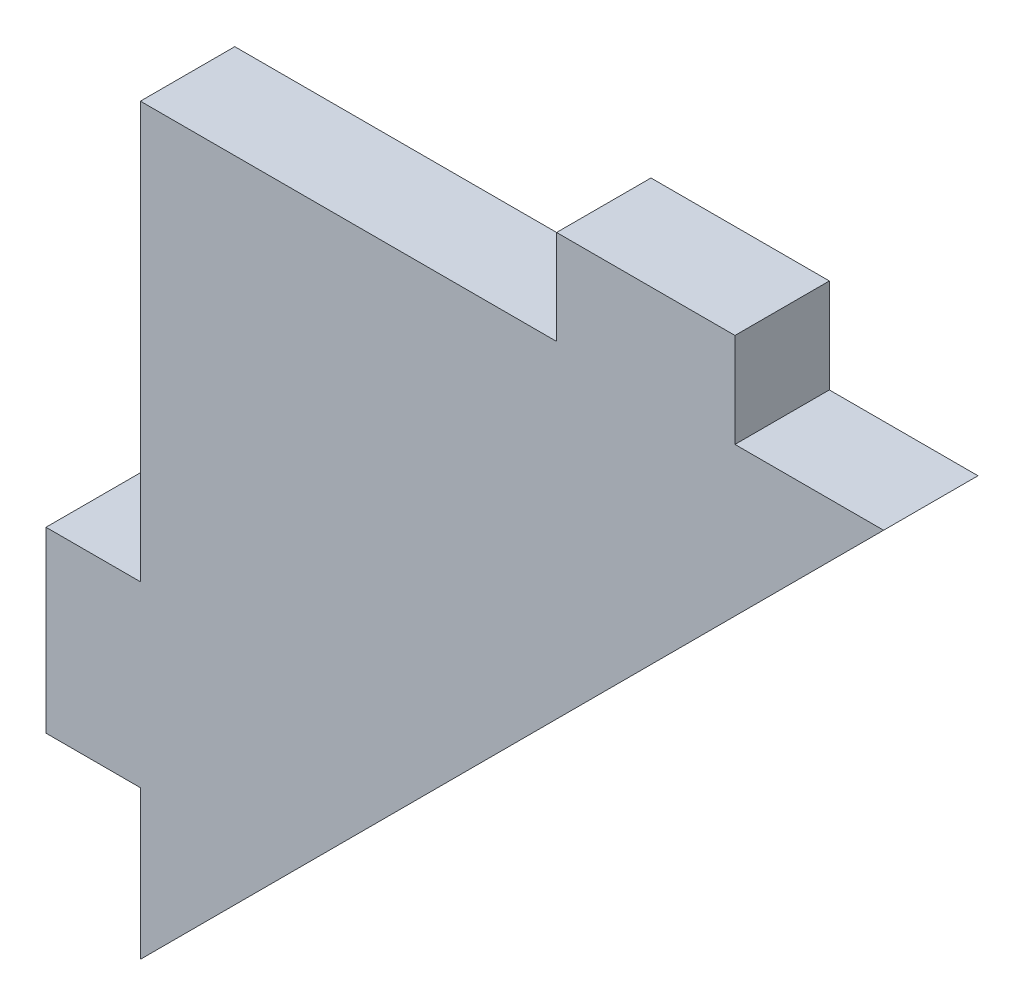
SolidWorks part; units mm, degrees
ref_plane "Front Plane" through (0, 0, 0) normal (0, 0, 1) x (1, 0, 0)
ref_plane "Top Plane" through (0, 0, 0) normal (0, 1, 0) x (1, 0, 0)
ref_plane "Right Plane" through (0, 0, 0) normal (1, 0, 0) x (0, 0, -1)
sketch "Sketch2" plane through (0, 0, 0) normal (0, 0, 1) x (1, 0, 0)
  line L0 (0, 25) -> (0, 11)
  line L1 (0, -14.8247) -> (0, 14.8247) construction
  line L2 (0, 25) -> (14, 25)
  line L3 (25, 25) -> (0, 0)
  line L4 (14, 28.175) -> (14, 25)
  line L5 (14, 28.175) -> (20, 28.175)
  line L6 (20, 28.175) -> (20, 25)
  line L7 (0, 11) -> (-3.175, 11)
  line L8 (-3.175, 11) -> (-3.175, 5)
  line L9 (-3.175, 5) -> (0, 5)
  line L10 (0, 5) -> (0, 0)
  line L11 (20, 25) -> (25, 25)
  dimension "D1" = 25
  dimension "D2" = 3.175
  dimension "D4" = 20
  dimension "D5" = 6
extrude "Boss-Extrude1" add sketch "Sketch2" along normal mid plane 3.175
